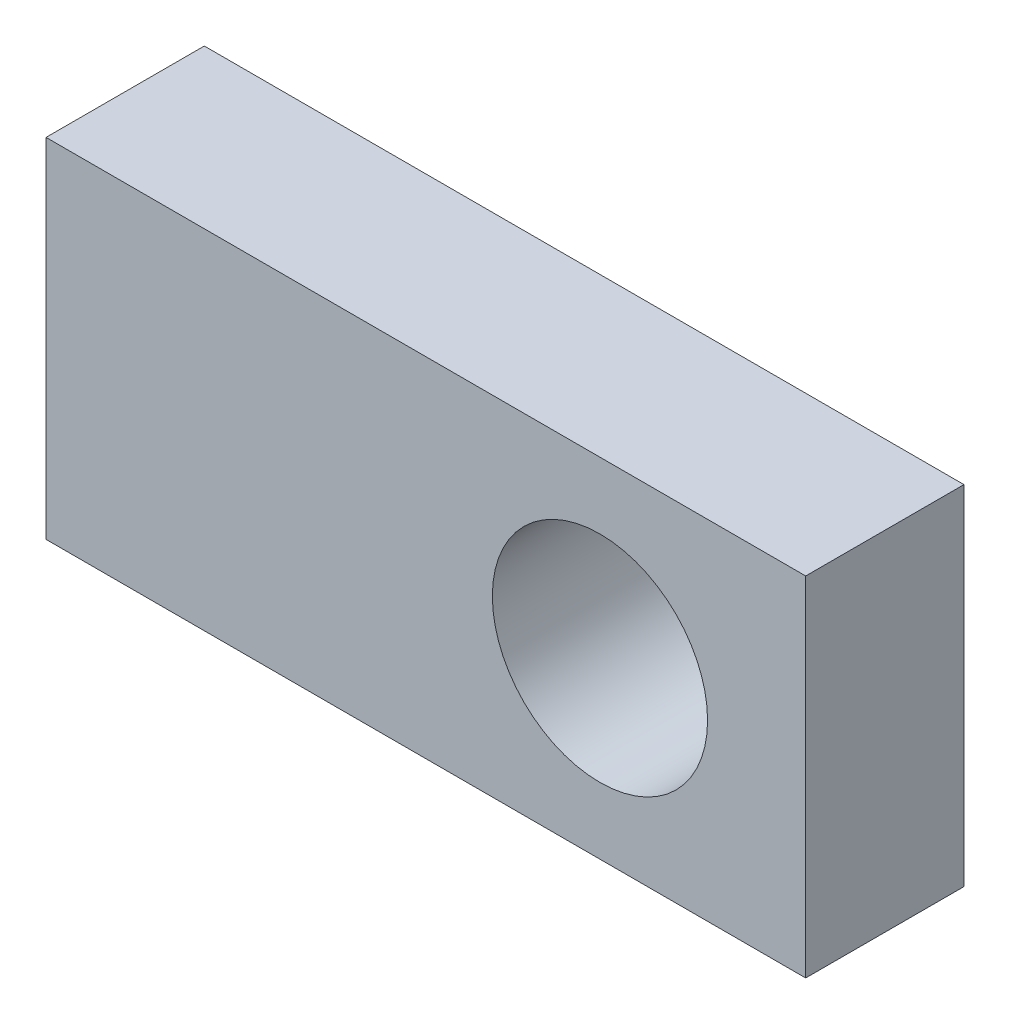
SolidWorks part; units mm, degrees
ref_plane "Vorne" through (0, 0, 0) normal (0, 0, 1) x (1, 0, 0)
ref_plane "Oben" through (0, 0, 0) normal (0, 1, 0) x (1, 0, 0)
ref_plane "Rechts" through (0, 0, 0) normal (1, 0, 0) x (0, 0, -1)
sketch "Skizze1" plane through (0, 0, 0) normal (0, 0, 1) x (1, 0, 0)
  line L0 (0, -55) -> (0, 55) construction
  line L1 (0, 5.5) -> (-24, 5.5)
  line L2 (0, 5.5) -> (0, -5.5)
  line L3 (0, -5.5) -> (-24, -5.5)
  line L4 (-24, 5.5) -> (-24, -5.5)
  line L5 (55, 0) -> (-55, 0) construction
  circle A0 centre (-6.5, 0) radius 3.4
  dimension "D4" = 6.8
  dimension "D6" = 5.5
  dimension "D1" = 24
  dimension "D2" = 11
  dimension "D3" = 5.5
  dimension "D5" = 6.5
extrude "Aufsatz-Linear austragen1" add sketch "Skizze1" along normal blind 5
cosmetic thread "Gewindedarstellung2"
